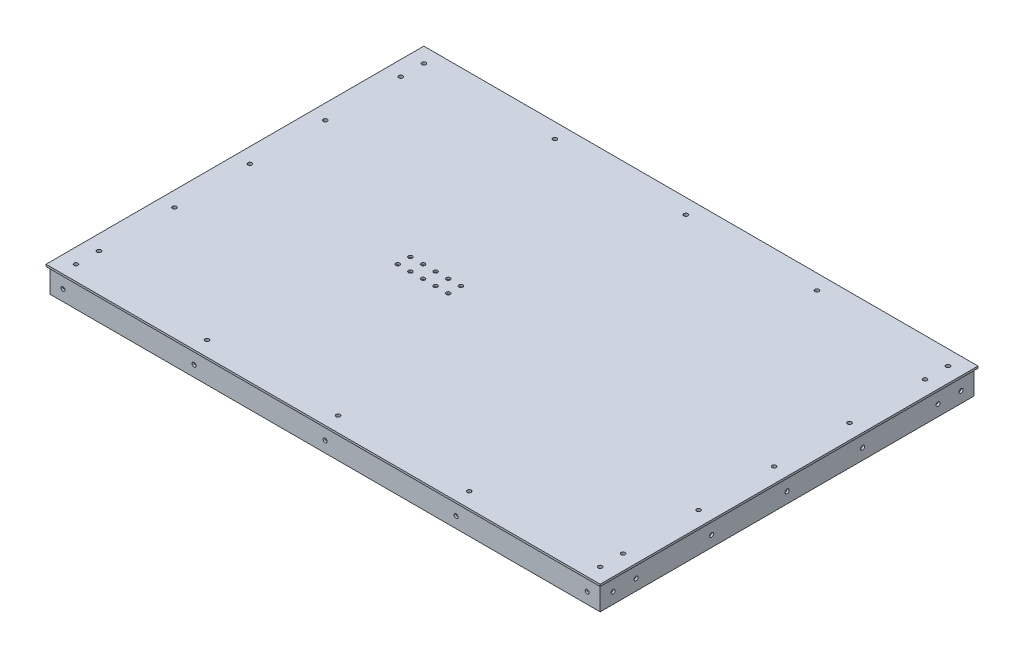
SolidWorks part; units mm, degrees
ref_plane "Plan de face" through (0, 0, 0) normal (0, 0, 1) x (1, 0, 0)
ref_plane "Plan de dessus" through (0, 0, 0) normal (0, 1, 0) x (1, 0, 0)
ref_plane "Plan de droite" through (0, 0, 0) normal (1, 0, 0) x (0, 0, -1)
sketch "Esquisse2" plane through (0, 0, 0) normal (0, 1, 0) x (1, 0, 0)
  line L1 (-236.836, 23.84) -> (161.889, 23.84)
  line L2 (-236.836, 23.84) -> (-236.836, -234.885)
  line L3 (-236.836, -234.885) -> (161.889, -234.885)
  line L4 (161.889, 23.84) -> (161.889, -234.885)
  line L5 (-255.886, 42.89) -> (180.939, 42.89)
  line L6 (-255.886, 42.89) -> (-255.886, -253.935)
  line L7 (-255.886, -253.935) -> (180.939, -253.935)
  line L8 (180.939, 42.89) -> (180.939, -253.935)
  dimension "D1" = 436.825
  dimension "D2" = 296.825
  dimension "D5" = 19.05
  dimension "D6" = 19.05
  dimension "D7" = 19.05
  dimension "D8" = 19.05
extrude "Boss.-Extru.2" add sketch "Esquisse2" along normal blind 1.5875
sketch "Esquisse3" plane through (0, 0, 0) normal (0, 1, 0) x (1, 0, 0)
  line L0 (180.939, 42.89) -> (-255.886, 42.89) construction
  line L1 (180.939, -253.935) -> (180.939, 42.89) construction
  line L2 (-255.886, 42.89) -> (-255.886, -253.935) construction
  line L3 (-255.886, -253.935) -> (180.939, -253.935) construction
  line L4 (180.939, 42.89) -> (-255.886, 42.89)
  line L5 (180.939, -253.935) -> (180.939, 42.89)
  line L6 (-255.886, 42.89) -> (-255.886, -253.935)
  line L7 (-255.886, -253.935) -> (180.939, -253.935)
  line L9 (-254.2985, 41.3025) -> (179.3515, 41.3025)
  line L10 (-254.2985, 41.3025) -> (-254.2985, -252.3475)
  line L11 (-254.2985, -252.3475) -> (179.3515, -252.3475)
  line L12 (179.3515, 41.3025) -> (179.3515, -252.3475)
  dimension "D1" = 1.5875
  dimension "D2" = 1.5875
  dimension "D3" = 1.5875
  dimension "D4" = 1.5875
extrude "Boss.-Extru.3" add sketch "Esquisse3" against normal blind 17.4625
sketch "Esquisse6" plane through (0, 1.5875, 0) normal (0, 1, 0) x (1, 0, 0)
  line L0 (161.889, 19.0813) -> (179.3515, 19.0813) construction
  line L1 (161.889, -234.885) -> (161.889, 23.84) construction
  line L2 (179.3515, -252.3475) -> (179.3515, 41.3025) construction
  line L3 (-231.0292, -234.885) -> (-231.0292, -252.3475) construction
  line L4 (-236.836, -234.885) -> (161.889, -234.885) construction
  line L6 (-236.836, -216.3082) -> (-254.2985, -216.3082) construction
  line L7 (-236.836, 23.84) -> (-236.836, -234.885) construction
  line L8 (-254.2985, 41.3025) -> (-254.2985, -252.3475) construction
  line L9 (-245.5673, -243.6162) -> (170.6202, -243.6162) construction
  line L10 (54.0935, 41.3025) -> (54.0935, 23.84) construction
  line L12 (161.889, 23.84) -> (-236.836, 23.84) construction
  line L13 (-37.4735, 32.5713) -> (170.6202, 32.5713) construction
  line L14 (-37.4735, 32.5713) -> (-245.5673, 32.5713) construction
  line L15 (170.6202, -165.4412) -> (170.6202, -45.6037) construction
  line L16 (170.6202, -105.5225) -> (170.6202, 14.315) construction
  line L17 (170.6202, -225.36) -> (170.6202, -105.5225) construction
  line L18 (-254.2985, -252.3475) -> (179.3515, -252.3475) construction
  line L19 (179.3515, 41.3025) -> (-254.2985, 41.3025) construction
  circle A7 centre (-245.5673, -243.6162) radius 1.5875
  circle A8 centre (170.6202, -243.6162) radius 1.5875
  circle A9 centre (-245.5673, 32.5713) radius 1.5875
  circle A10 centre (170.6202, 32.5713) radius 1.5875
  circle A11 centre (-141.5204, -243.6162) radius 1.5875
  circle A12 centre (66.5733, -243.6162) radius 1.5875
  circle A13 centre (66.5733, 32.5713) radius 1.5875
  circle A14 centre (-141.5204, 32.5713) radius 1.5875
  circle A15 centre (170.6202, -45.6037) radius 1.5875
  circle A16 centre (-37.4735, -243.6162) radius 1.5875
  circle A17 centre (-37.4735, 32.5713) radius 1.5875
  circle A18 centre (170.6202, -165.4412) radius 1.5875
  circle A19 centre (-245.5673, -165.4412) radius 1.5875
  circle A20 centre (-245.5673, -45.6037) radius 1.5875
  circle A21 centre (-245.5673, -225.36) radius 1.5875
  circle A22 centre (-245.5673, 14.315) radius 1.5875
  circle A23 centre (170.6202, 14.315) radius 1.5875
  circle A24 centre (170.6202, -225.36) radius 1.5875
  circle A25 centre (-245.5673, -105.5225) radius 1.5875
  circle A26 centre (170.6202, -105.5225) radius 1.5875
  point P0 (0, 0)
  point P2 (0, 0)
  point P3 (0, 0)
  point P42 (-231.0292, -243.6162)
  point P49 (170.6202, 19.0813)
  point P64 (-245.5673, -216.3082)
  point P65 (54.0935, 32.5713)
  point P66 (-37.4735, -243.6162)
  point P73 (66.5733, 32.5713)
  point P74 (170.6202, -105.5225)
  point P81 (-141.5204, 32.5713)
  point P82 (179.3515, -105.5225)
  dimension "D1" = 3.175
  dimension "D2" = 18.2563
extrude "Enlèv. mat.-Extru.1" cut sketch "Esquisse6" against normal up to next
sketch "Esquisse7" plane through (179.3515, 0, 0) normal (-1, 0, 0) x (0, 0, 1)
  line L0 (245.2037, 1.5875) -> (242.0287, 1.5875) construction
  line L1 (-30.9838, 1.5875) -> (-34.1588, 1.5875) construction
  line L2 (-12.7275, 1.5875) -> (-15.9025, 1.5875) construction
  line L3 (47.1912, 1.5875) -> (44.0162, 1.5875) construction
  line L4 (107.11, 1.5875) -> (103.935, 1.5875) construction
  line L5 (167.0287, 1.5875) -> (163.8537, 1.5875) construction
  line L6 (226.9475, 1.5875) -> (223.7725, 1.5875) construction
  line L7 (245.2037, 1.5875) -> (242.0287, 1.5875) construction
  line L8 (-30.9838, 1.5875) -> (-34.1588, 1.5875) construction
  line L9 (-12.7275, 1.5875) -> (-15.9025, 1.5875) construction
  line L10 (47.1912, 1.5875) -> (44.0162, 1.5875) construction
  line L11 (107.11, 1.5875) -> (103.935, 1.5875) construction
  line L12 (167.0287, 1.5875) -> (163.8537, 1.5875) construction
  line L13 (226.9475, 1.5875) -> (223.7725, 1.5875) construction
  line L14 (6.3143, 0) -> (6.3143, -17.4625) construction
  line L16 (252.3475, -17.4625) -> (-41.3025, -17.4625) construction
  line L17 (252.3475, 0) -> (-41.3025, 0) construction
  circle A0 centre (-32.5713, -8.7312) radius 1.5875
  circle A1 centre (-14.315, -8.7312) radius 1.5875
  circle A2 centre (45.6037, -8.7312) radius 1.5875
  circle A3 centre (105.5225, -8.7312) radius 1.5875
  circle A4 centre (165.4412, -8.7312) radius 1.5875
  circle A5 centre (225.36, -8.7312) radius 1.5875
  circle A6 centre (243.6162, -8.7312) radius 1.5875
  point P28 (6.3143, -8.7312)
  point P31 (0, 0)
  point P35 (225.36, 1.5875)
  point P36 (243.6162, 1.5875)
  point P37 (165.4412, 1.5875)
  point P38 (0, 0)
  point P39 (105.5225, 1.5875)
  point P40 (45.6037, 1.5875)
  point P41 (-14.315, 1.5875)
  point P42 (-32.5713, 1.5875)
  dimension "D1" = 3.175
extrude "Enlèv. mat.-Extru.2" cut sketch "Esquisse7" against normal up to next
sketch "Esquisse8" plane through (-254.2985, 0, 0) normal (1, 0, 0) x (0, 0, -1)
  line L0 (34.1588, 1.5875) -> (30.9838, 1.5875) construction
  line L1 (15.9025, 1.5875) -> (12.7275, 1.5875) construction
  line L2 (-44.0162, 1.5875) -> (-47.1912, 1.5875) construction
  line L3 (-103.935, 1.5875) -> (-107.11, 1.5875) construction
  line L4 (-163.8537, 1.5875) -> (-167.0287, 1.5875) construction
  line L5 (-242.0287, 1.5875) -> (-245.2037, 1.5875) construction
  line L6 (-223.7725, 1.5875) -> (-226.9475, 1.5875) construction
  line L7 (34.1588, 1.5875) -> (30.9838, 1.5875) construction
  line L8 (15.9025, 1.5875) -> (12.7275, 1.5875) construction
  line L9 (-44.0162, 1.5875) -> (-47.1912, 1.5875) construction
  line L10 (-103.935, 1.5875) -> (-107.11, 1.5875) construction
  line L11 (-163.8537, 1.5875) -> (-167.0287, 1.5875) construction
  line L12 (-242.0287, 1.5875) -> (-245.2037, 1.5875) construction
  line L13 (-223.7725, 1.5875) -> (-226.9475, 1.5875) construction
  line L14 (25.8822, -17.4625) -> (25.8822, 0) construction
  line L15 (41.3025, -17.4625) -> (-252.3475, -17.4625) construction
  line L17 (41.3025, 0) -> (-252.3475, 0) construction
  circle A0 centre (-243.6162, -8.7312) radius 1.5875
  circle A1 centre (-225.36, -8.7312) radius 1.5875
  circle A2 centre (-165.4412, -8.7312) radius 1.5875
  circle A3 centre (-105.5225, -8.7312) radius 1.5875
  circle A4 centre (-45.6037, -8.7312) radius 1.5875
  circle A5 centre (14.315, -8.7312) radius 1.5875
  circle A6 centre (32.5713, -8.7312) radius 1.5875
  point P28 (25.8822, -8.7312)
  point P33 (0, 0)
  point P35 (0, 0)
  point P36 (32.5713, 1.5875)
  point P38 (14.315, 1.5875)
  point P39 (-45.6037, 1.5875)
  point P40 (-105.5225, 1.5875)
  point P41 (-165.4412, 1.5875)
  point P43 (-225.36, 1.5875)
  point P45 (-243.6162, 1.5875)
  dimension "D1" = 3.175
extrude "Enlèv. mat.-Extru.3" cut sketch "Esquisse8" against normal up to next
sketch "Esquisse9" plane through (0, 0, -41.3025) normal (0, 0, 1) x (1, 0, 0)
  line L0 (172.2077, 1.5875) -> (169.0327, 1.5875) construction
  line L1 (68.1608, 1.5875) -> (64.9858, 1.5875) construction
  line L2 (-35.886, 1.5875) -> (-39.061, 1.5875) construction
  line L3 (-139.9329, 1.5875) -> (-143.1079, 1.5875) construction
  line L4 (-243.9798, 1.5875) -> (-247.1548, 1.5875) construction
  line L5 (172.2077, 1.5875) -> (169.0327, 1.5875) construction
  line L6 (68.1608, 1.5875) -> (64.9858, 1.5875) construction
  line L7 (-35.886, 1.5875) -> (-39.061, 1.5875) construction
  line L8 (-139.9329, 1.5875) -> (-143.1079, 1.5875) construction
  line L9 (-243.9798, 1.5875) -> (-247.1548, 1.5875) construction
  line L10 (73.1782, -17.4625) -> (73.1782, 0) construction
  line L11 (179.3515, -17.4625) -> (-254.2985, -17.4625) construction
  line L13 (179.3515, 0) -> (-254.2985, 0) construction
  circle A0 centre (-245.5673, -8.7312) radius 1.5875
  circle A1 centre (-141.5204, -8.7312) radius 1.5875
  circle A2 centre (-37.4735, -8.7312) radius 1.5875
  circle A3 centre (66.5733, -8.7312) radius 1.5875
  circle A4 centre (170.6202, -8.7312) radius 1.5875
  point P20 (73.1782, -8.7312)
  point P25 (0, 0)
  point P27 (170.6202, 1.5875)
  point P28 (66.5733, 1.5875)
  point P29 (-37.4735, 1.5875)
  point P30 (-141.5204, 1.5875)
  point P31 (-245.5673, 1.5875)
  dimension "D1" = 3.175
extrude "Enlèv. mat.-Extru.4" cut sketch "Esquisse9" against normal up to next
sketch "Esquisse10" plane through (0, 0, -42.89) normal (0, 0, -1) x (-1, 0, 0)
  line L0 (37.4735, -8.7312) -> (141.5204, -8.7312) construction
  line L1 (53.747, -4.8) -> (125.247, -4.8) construction
  circle A0 centre (53.747, -4.8) radius 2
  circle A1 centre (125.247, -4.8) radius 2
  point P4 (89.497, -4.8)
  point P9 (89.497, -8.7312)
  dimension "D2" = 4
  dimension "D1" = 71.5
  dimension "D3" = 3.9312
extrude "Enlèv. mat.-Extru.6" cut sketch "Esquisse10" against normal up to next
sketch "Esquisse1" plane through (0, 1.5875, 0) normal (0, 1, 0) x (1, 0, 0)
  line L0 (-255.886, 42.89) -> (-255.886, -253.935) construction
  line L1 (-257.4735, 44.4775) -> (182.5265, 44.4775)
  line L2 (-257.4735, 44.4775) -> (-257.4735, -255.5225)
  line L3 (-257.4735, -255.5225) -> (182.5265, -255.5225)
  line L4 (182.5265, 44.4775) -> (182.5265, -255.5225)
  line L5 (-255.886, -253.935) -> (180.939, -253.935) construction
  circle A0 centre (170.6202, -45.6037) radius 1.5875 construction
  circle A1 centre (170.6202, -105.5225) radius 1.5875 construction
  circle A2 centre (170.6202, -165.4412) radius 1.5875 construction
  circle A3 centre (170.6202, -225.36) radius 1.5875 construction
  circle A4 centre (170.6202, -243.6162) radius 1.5875 construction
  circle A5 centre (170.6202, 14.315) radius 1.5875 construction
  circle A6 centre (170.6202, 32.5713) radius 1.5875 construction
  circle A7 centre (66.5733, 32.5713) radius 1.5875 construction
  circle A8 centre (-37.4735, 32.5713) radius 1.5875 construction
  circle A9 centre (-141.5204, 32.5713) radius 1.5875 construction
  circle A11 centre (-245.5673, 32.5713) radius 1.5875 construction
  circle A12 centre (-245.5673, 14.315) radius 1.5875 construction
  circle A13 centre (-245.5673, -45.6037) radius 1.5875 construction
  circle A14 centre (-245.5673, -105.5225) radius 1.5875 construction
  circle A15 centre (-245.5673, -165.4412) radius 1.5875 construction
  circle A16 centre (-245.5673, -225.36) radius 1.5875 construction
  circle A17 centre (-245.5673, -243.6162) radius 1.5875 construction
  circle A25 centre (66.5733, -243.6162) radius 1.5875 construction
  circle A26 centre (-37.4735, -243.6162) radius 1.5875 construction
  circle A27 centre (-141.5204, -243.6162) radius 1.5875 construction
  circle A35 centre (66.5733, -243.6162) radius 1.5875
  circle A36 centre (-37.4735, -243.6162) radius 1.5875
  circle A37 centre (-141.5204, -243.6162) radius 1.5875
  circle A38 centre (-245.5673, -243.6162) radius 1.5875
  circle A39 centre (-245.5673, -225.36) radius 1.5875
  circle A40 centre (-245.5673, -165.4412) radius 1.5875
  circle A41 centre (-245.5673, -105.5225) radius 1.5875
  circle A42 centre (-245.5673, -45.6037) radius 1.5875
  circle A43 centre (-245.5673, 14.315) radius 1.5875
  circle A44 centre (-245.5673, 32.5713) radius 1.5875
  circle A46 centre (-141.5204, 32.5713) radius 1.5875
  circle A47 centre (-37.4735, 32.5713) radius 1.5875
  circle A48 centre (66.5733, 32.5713) radius 1.5875
  circle A49 centre (170.6202, 32.5713) radius 1.5875
  circle A50 centre (170.6202, 14.315) radius 1.5875
  circle A51 centre (170.6202, -243.6162) radius 1.5875
  circle A52 centre (170.6202, -225.36) radius 1.5875
  circle A53 centre (170.6202, -165.4412) radius 1.5875
  circle A54 centre (170.6202, -105.5225) radius 1.5875
  circle A55 centre (170.6202, -45.6037) radius 1.5875
  dimension "D1" = 440
  dimension "D2" = 300
  dimension "D3" = 1.5875
  dimension "D4" = 1.5875
extrude "Boss.-Extru.7" add sketch "Esquisse1" along normal blind 1.5875
sketch "Esquisse16" plane through (0, 0, 252.3475) normal (0, 0, -1) x (-1, 0, 0)
  line L0 (-172.2077, 0) -> (-169.0327, 0) construction
  line L1 (-68.1608, 0) -> (-64.9858, 0) construction
  line L2 (35.886, 0) -> (39.061, 0) construction
  line L3 (139.9329, 0) -> (143.1079, 0) construction
  line L4 (243.9798, 0) -> (247.1548, 0) construction
  line L5 (-172.2077, 0) -> (-169.0327, 0) construction
  line L6 (-68.1608, 0) -> (-64.9858, 0) construction
  line L7 (35.886, 0) -> (39.061, 0) construction
  line L8 (139.9329, 0) -> (143.1079, 0) construction
  line L9 (243.9798, 0) -> (247.1548, 0) construction
  line L10 (-89.0751, -17.4625) -> (-89.0751, 0) construction
  line L11 (254.2985, -17.4625) -> (-179.3515, -17.4625) construction
  line L12 (254.2985, 0) -> (-179.3515, 0) construction
  circle A0 centre (245.5673, -8.7312) radius 1.5875
  circle A1 centre (141.5204, -8.7312) radius 1.5875
  circle A2 centre (37.4735, -8.7312) radius 1.5875
  circle A3 centre (-66.5733, -8.7312) radius 1.5875
  circle A4 centre (-170.6202, -8.7312) radius 1.5875
  point P20 (-89.0751, -8.7312)
  point P27 (-170.6202, 0)
  point P29 (-66.5733, 0)
  point P31 (37.4735, 0)
  point P32 (141.5204, 0)
  point P33 (245.5673, 0)
  dimension "D1" = 3.175
extrude "Enlèv. mat.-Extru.10" cut sketch "Esquisse16" against normal up to next
sketch "Esquisse17" plane through (0, 3.175, 0) normal (0, 1, 0) x (1, 0, 0)
  line L0 (-257.4735, -255.5225) -> (182.5265, -255.5225) construction
  line L1 (-257.4735, 44.4775) -> (-257.4735, -255.5225) construction
  circle A0 centre (-77.7923, -115.8412) radius 1.5875
  circle A1 centre (-87.7923, -115.8412) radius 1.5875
  circle A2 centre (-97.7923, -115.8412) radius 1.5875
  circle A3 centre (-107.7923, -115.8412) radius 1.5875
  circle A4 centre (-117.7923, -115.8412) radius 1.5875
  circle A5 centre (-87.7923, -105.8412) radius 1.5875
  circle A6 centre (-97.7923, -105.8412) radius 1.5875
  circle A7 centre (-107.7923, -105.8412) radius 1.5875
  circle A8 centre (-117.7923, -105.8412) radius 1.5875
  circle A9 centre (-77.7923, -105.8412) radius 1.5875
  point P23 (-97.7923, -115.8412)
  dimension "D1" = 3.175
  dimension "D4" = 159.6813
  dimension "D5" = 139.6812
  dimension "D3" = 5
  dimension "D2" = 2
extrude "Enlèv. mat.-Extru.11" cut sketch "Esquisse17" against normal up to next
